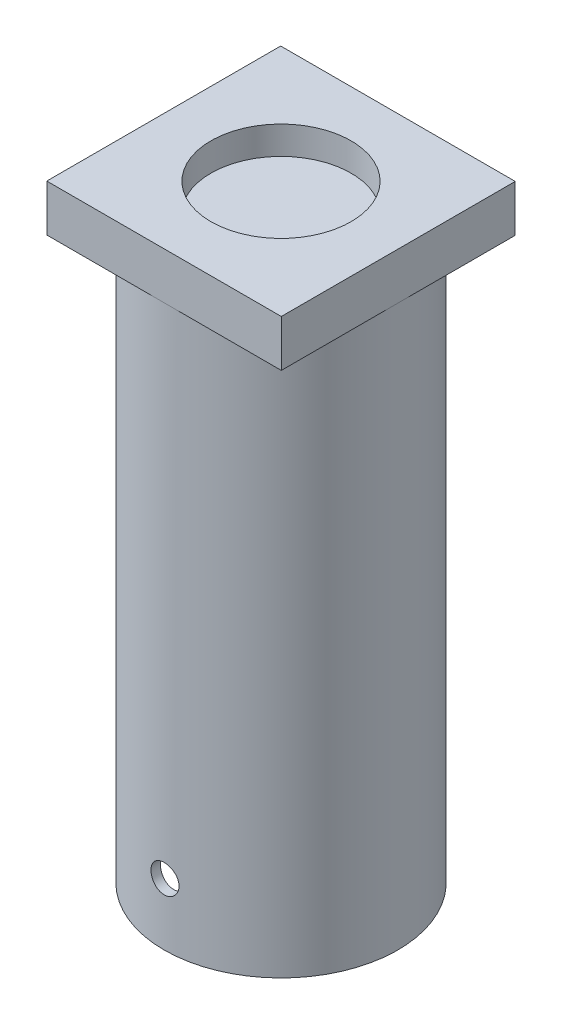
SolidWorks part; units mm, degrees
material "ABS"
ref_plane "Спереди" through (0, 0, 0) normal (0, 0, 1) x (1, 0, 0)
ref_plane "Сверху" through (0, 0, 0) normal (0, 1, 0) x (1, 0, 0)
ref_plane "Справа" through (0, 0, 0) normal (1, 0, 0) x (0, 0, -1)
other "Configuration Table"
sketch "Sketch1" plane through (0, 0, 0) normal (0, 1, 0) x (1, 0, 0)
  circle A0 centre (0, 0) radius 12.5
  circle A1 centre (0, 0) radius 11.5
  dimension "D1" = 23
  dimension "D2" = 25
extrude "Boss-Extrude1" add sketch "Sketch1" along normal blind 60
sketch "Sketch2" plane through (0, 0, 0) normal (0, 0, 1) x (1, 0, 0)
  line L0 (-12.5, 6.62) -> (12.5, 6.62) construction
  line L1 (-12.5, 60) -> (-12.5, 0) construction
  line L2 (12.5, 0) -> (12.5, 60) construction
  line L3 (11.5, 60) -> (-11.5, 60) construction
  circle A0 centre (0, 6.62) radius 1.5
  dimension "D2" = 3
  dimension "D1" = 53.38
extrude "Cut-Extrude1" cut sketch "Sketch2" along normal up to surface (12.4097 mm away)
sketch "Sketch3" plane through (0, 60, 0) normal (0, 1, 0) x (1, 0, 0)
  line L1 (-12.5487, 12.5154) -> (12.5487, 12.5154)
  line L2 (-12.5487, 12.5154) -> (-12.5487, -12.5154)
  line L3 (-12.5487, -12.5154) -> (12.5487, -12.5154)
  line L4 (12.5487, 12.5154) -> (12.5487, -12.5154)
  line L5 (-12.5487, 12.5154) -> (12.5487, -12.5154) construction
  line L6 (-12.5487, -12.5154) -> (12.5487, 12.5154) construction
  point P0 (0, 0)
extrude "Boss-Extrude2" add sketch "Sketch3" along normal blind 5
sketch "Sketch4" plane through (0, 65, 0) normal (0, 1, 0) x (1, 0, 0)
  circle A0 centre (0, 0) radius 7.5
  dimension "D1" = 15
extrude "Cut-Extrude2" cut sketch "Sketch4" against normal blind 3
